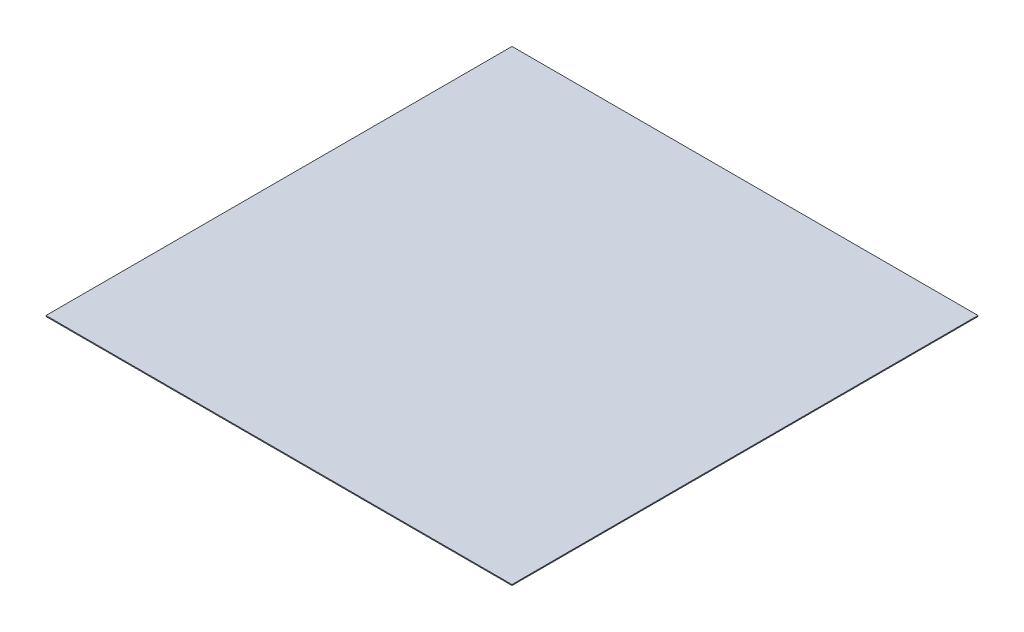
SolidWorks part; units mm, degrees
ref_plane "Front Plane" through (0, 0, 0) normal (0, 0, 1) x (1, 0, 0)
ref_plane "Top Plane" through (0, 0, 0) normal (0, 1, 0) x (1, 0, 0)
ref_plane "Right Plane" through (0, 0, 0) normal (1, 0, 0) x (0, 0, -1)
sketch "Sketch1" plane through (0, 0, 0) normal (0, 1, 0) x (1, 0, 0)
  line L1 (-5000, 5000) -> (5000, 5000)
  line L2 (-5000, 5000) -> (-5000, -5000)
  line L3 (-5000, -5000) -> (5000, -5000)
  line L4 (5000, 5000) -> (5000, -5000)
  line L5 (-5000, 5000) -> (5000, -5000) construction
  line L6 (-5000, -5000) -> (5000, 5000) construction
  point P0 (0, 0)
  dimension "D1" = 10000
  dimension "D2" = 10000
extrude "Boss-Extrude1" add sketch "Sketch1" along normal blind 20
